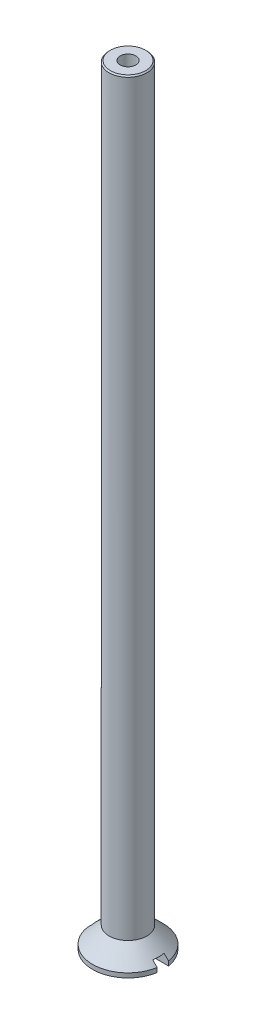
SolidWorks part; units mm, degrees
material "Латунь"
ref_plane "Спереди" through (0, 0, 0) normal (0, 0, 1) x (1, 0, 0)
ref_plane "Сверху" through (0, 0, 0) normal (0, 1, 0) x (1, 0, 0)
ref_plane "Справа" through (0, 0, 0) normal (1, 0, 0) x (0, 0, -1)
sketch "Эскиз1" plane through (0, 0, 0) normal (0, 1, 0) x (1, 0, 0)
  circle A0 centre (0, 0) radius 1.5
  dimension "D1" = 3
extrude "Бобышка-Вытянуть1" add sketch "Эскиз1" along normal blind 61
sketch "Эскиз2" plane through (0, 0, 0) normal (1, 0, 0) x (0, 0, -1)
  line L0 (0, 0) -> (0, 50000) construction
  line L1 (0, 3.15) -> (-2.8, 0.35)
  line L2 (-2.8, 0.35) -> (-2.8, 0)
  line L3 (-2.8, 0) -> (0, 0)
  line L5 (0, 3.15) -> (0, 0)
  dimension "D1" = 0.35
  dimension "D2" = 45
  dimension "D3" = 5.6
revolve "Повернуть1" add sketch "Эскиз2" angle 360 about L0
sketch "Эскиз3" plane through (0, 0, 0) normal (1, 0, 0) x (0, 0, -1)
  line L0 (0, 0) -> (0, 50000) construction
  line L1 (-3.15, 0) -> (3.15, 0) construction
  line L2 (-0.45, 0) -> (0.45, 0)
  line L3 (-0.45, 0) -> (-0.45, 0.7)
  line L4 (-0.45, 0.7) -> (0.45, 0.7)
  line L5 (0.45, 0) -> (0.45, 0.7)
  dimension "D1" = 0.9
  dimension "D2" = 0.7
extrude "Вырез-Вытянуть1" cut sketch "Эскиз3" against normal through all both and the other way through all
chamfer "Фаска1" distance 0.1 angle 45 1 edges at (0, 61, 1.5)
hole_wizard "Отверстие обработанное метчиком M1,61" positions "Эскиз5" profile "Эскиз4" tap size "M1,6" standard "GOST"
sketch "Эскиз5" plane through (0, 61, 0) normal (0, 1, 0) x (1, 0, 0)
  point P0 (0, 0)
sketch "Эскиз4" plane through (0, 61, 0) normal (1, 0, 0) x (0, 0, 1)
  line L0 (0, 0) -> (0, 7.3755)
  line L1 (0, 7.3755) -> (0.625, 7)
  line L2 (0.625, 7) -> (0.625, 0)
  line L5 (0.625, 0) -> (0, 0)
  line L10 (0, 7.3755) -> (-0.625, 7) construction
  line L11 (0, -6.35) -> (0, 107.95) construction
  dimension "Диаметр сверла" = 1.25
  dimension "Глубина сверла" = 7
  dimension "Угол заточки сверла" = 118
cosmetic thread "Отверстие резьбы1" parameters "D1"=5, "D2"=1.6
